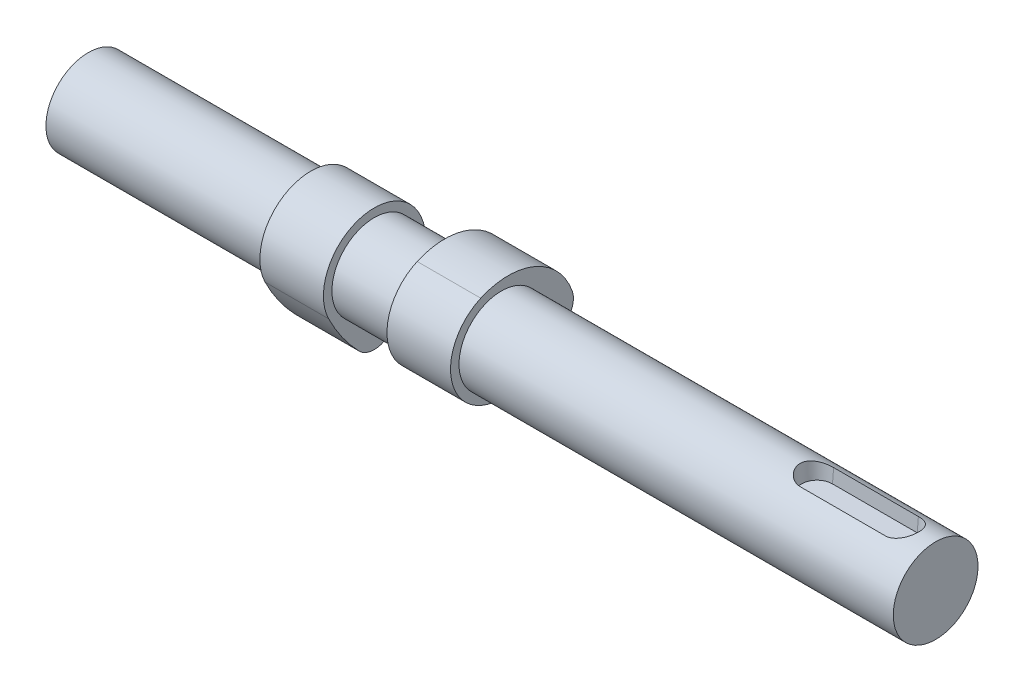
SolidWorks part; units mm, degrees
ref_plane "Front Plane" through (0, 0, 0) normal (0, 0, 1) x (1, 0, 0)
ref_plane "Top Plane" through (0, 0, 0) normal (0, 1, 0) x (1, 0, 0)
ref_plane "Right Plane" through (0, 0, 0) normal (1, 0, 0) x (0, 0, -1)
sketch "Sketch1" plane through (0, 0, 0) normal (1, 0, 0) x (0, 0, -1)
  circle A0 centre (0, 0) radius 10
  dimension "D1" = 20
extrude "Boss-Extrude1" add sketch "Sketch1" along normal blind 125 and the other way blind 75
sketch "Sketch2" plane through (0, 0, 0) normal (1, 0, 0) x (0, 0, -1)
  arc A1 (-4.8671, 10.9687) -> (5.3062, -10.7631) centre (0, 0) ccw
  arc A2 (-4.8671, 10.9687) -> (16.7127, 1.6619) centre (1.6224, -3.6562) cw
  arc A3 (5.3062, -10.7631) -> (15.4795, -3.5877) centre (-12.3812, 25.1139) ccw
  arc A4 (16.7127, 1.6619) -> (15.4795, -3.5877) centre (11.997, 0) cw
  dimension "D1" = 5
  dimension "D2" = 40
  dimension "D3" = 16
  dimension "D4" = 24
  dimension "D5" = 12.5
extrude "Boss-Extrude2" add sketch "Sketch2" along normal mid plane 15 from offset 15 separate body
mirror "Mirror1" about plane through (0, 0, 0) normal (1, 0, 0) of bodies 102
move or copy body "Body-Move/Copy1" bodies to move or copy 103 copy no rotation origin (0, 0, 0) rotation axis (-1, 0, 0) rotation angle 90
sketch "Sketch3" plane through (0, 0, 0) normal (0, 1, 0) x (1, 0, 0)
  line L0 (125, 0) -> (75.2171, 0) construction
  line L1 (125, -10) -> (125, 10) construction
  line L2 (97, 0) -> (117, 0) construction
  line L3 (97, 4) -> (117, 4)
  line L4 (97, -4) -> (117, -4)
  arc A0 (97, 4) -> (97, -4) centre (97, 0) ccw
  arc A1 (117, -4) -> (117, 4) centre (117, 0) ccw
  point P7 (107, 0)
  dimension "D1" = 4
  dimension "D2" = 20
  dimension "D3" = 8
extrude "Cut-Extrude1" cut sketch "Sketch3" against normal blind 4 draft 5 from offset 10
